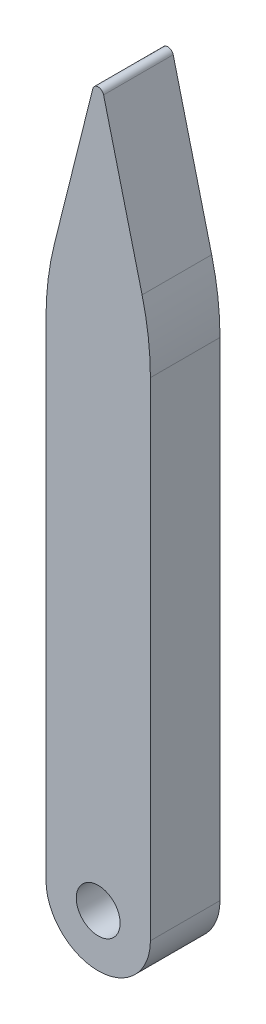
SolidWorks part; units mm, degrees
material "Acrylic (Medium-high impact)"
ref_plane "Front" through (0, 0, 0) normal (0, 0, 1) x (1, 0, 0)
ref_plane "Top" through (0, 0, 0) normal (0, 1, 0) x (1, 0, 0)
ref_plane "Right" through (0, 0, 0) normal (1, 0, 0) x (0, 0, -1)
sketch "Sketch1" plane through (0, 0, 0) normal (0, 0, 1) x (1, 0, 0)
  line L0 (-1.1906, -6) -> (-1.1906, 5.9062)
  line L1 (-1.1906, 5.9062) -> (0, 10.6687)
  line L2 (0, 10.6687) -> (0, -6) construction
  line L3 (0, -6) -> (0, -7.1906) construction
  line L4 (1.1906, -6) -> (1.1906, 5.9062)
  line L5 (1.1906, 5.9062) -> (0, 10.6687)
  arc A1 (-1.1906, -6) -> (1.1906, -6) centre (0, -6) ccw
  circle A3 centre (0, -6) radius 0.5
  circle A4 centre (0, -6) radius 0.5
  dimension "D1" = 0
  dimension "D2" = 2.3813
  dimension "D3" = 4.7625
  dimension "D4" = 16.6687
extrude "Boss-Extrude1" add sketch "Sketch1" against normal blind 1.5875
fillet "Fillet1" radius 6.35 2 edges at (1.1906, 5.9062, -0.7937) (-1.1906, 5.9062, -0.7937)
fillet "Fillet2" radius 0.127 1 edges at (0, 10.6687, -0.7937)
